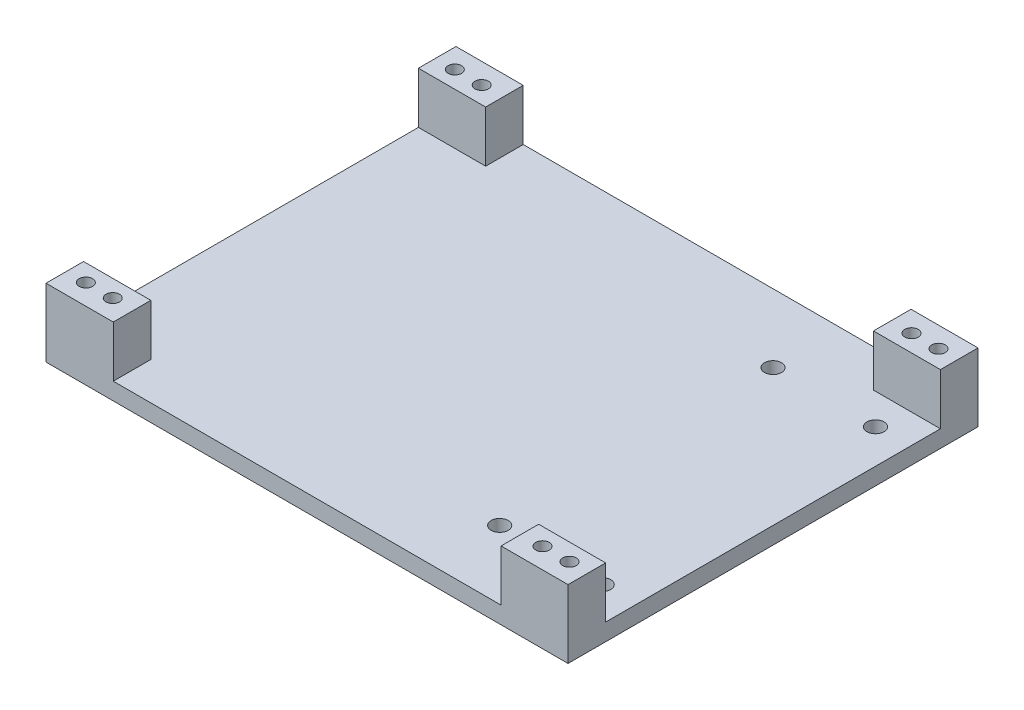
SolidWorks part; units mm, degrees
ref_plane "Front Plane" through (0, 0, 0) normal (0, 0, 1) x (1, 0, 0)
ref_plane "Top Plane" through (0, 0, 0) normal (0, 1, 0) x (1, 0, 0)
ref_plane "Right Plane" through (0, 0, 0) normal (1, 0, 0) x (0, 0, -1)
sketch "Sketch2" plane through (0, 0, 0) normal (0, 1, 0) x (1, 0, 0)
  line L1 (-140.716, 56.5856) -> (53.34, 56.5856)
  line L2 (-140.716, 56.5856) -> (-140.716, -95.8144)
  line L3 (-140.716, -95.8144) -> (53.34, -95.8144)
  line L4 (53.34, 56.5856) -> (53.34, -95.8144)
  dimension "D1" = 194.056
  dimension "D2" = 152.4
extrude "Boss-Extrude1" add sketch "Sketch2" along normal blind 6.35
sketch "Sketch3" plane through (0, 6.35, 0) normal (0, 1, 0) x (1, 0, 0)
  line L1 (53.34, -95.8144) -> (53.34, 56.5856) construction
  line L2 (-140.716, -95.8144) -> (53.34, -95.8144) construction
  line L3 (53.34, 56.5856) -> (-140.716, 56.5856) construction
  circle A0 centre (2.54, -70.4144) radius 3.175
  circle A1 centre (2.54, 31.1856) radius 3.175
  circle A2 centre (40.64, 31.1856) radius 3.175
  circle A3 centre (40.64, -70.4144) radius 3.175
  dimension "D1" = 6.35
  dimension "D2" = 38.1
  dimension "D3" = 12.7
  dimension "1" = 25.4
  dimension "D5" = 25.4
extrude "Cut-Extrude1" cut sketch "Sketch3" against normal blind 6.35
sketch "Sketch4" plane through (0, 6.35, 0) normal (0, 1, 0) x (1, 0, 0)
  line L1 (53.34, -95.8144) -> (28.448, -95.8144)
  line L2 (53.34, -95.8144) -> (53.34, -81.8444)
  line L3 (53.34, -81.8444) -> (28.448, -81.8444)
  line L4 (28.448, -95.8144) -> (28.448, -81.8444)
  line L5 (-140.716, -95.8144) -> (-115.716, -95.8144)
  line L6 (-140.716, -95.8144) -> (-140.716, -81.8444)
  line L7 (-140.716, -81.8444) -> (-115.716, -81.8444)
  line L8 (-115.716, -95.8144) -> (-115.716, -81.8444)
  line L9 (-140.716, 56.5856) -> (-115.716, 56.5856)
  line L10 (-140.716, 56.5856) -> (-140.716, 42.6156)
  line L11 (-140.716, 42.6156) -> (-115.716, 42.6156)
  line L12 (-115.716, 56.5856) -> (-115.716, 42.6156)
  line L13 (53.34, 56.5856) -> (28.448, 56.5856)
  line L14 (53.34, 56.5856) -> (53.34, 42.6156)
  line L15 (53.34, 42.6156) -> (28.448, 42.6156)
  line L16 (28.448, 56.5856) -> (28.448, 42.6156)
  dimension "D1" = 13.97
  dimension "1in" = 25
  dimension "D2" = 13.97
  dimension "D3" = 24.892
extrude "Boss-Extrude2" add sketch "Sketch4" along normal blind 19.05
sketch "Sketch5" plane through (0, 25.4, 0) normal (0, 1, 0) x (1, 0, 0)
  line L1 (-115.716, 56.5856) -> (-140.716, 56.5856) construction
  line L2 (-140.716, -95.8144) -> (-115.716, -95.8144) construction
  line L5 (53.34, 56.5856) -> (28.448, 56.5856) construction
  line L6 (28.448, -95.8144) -> (53.34, -95.8144) construction
  line L7 (-115.716, 42.6156) -> (-115.716, 56.5856) construction
  line L8 (28.448, 56.5856) -> (28.448, 42.6156) construction
  line L9 (28.448, -81.8444) -> (28.448, -95.8144) construction
  circle A0 centre (-133.526, -88.1944) radius 2.5
  circle A1 centre (-123.526, -88.1944) radius 2.5
  circle A2 centre (-133.526, 48.9656) radius 2.5
  circle A3 centre (-123.526, 48.9656) radius 2.5
  circle A4 centre (36.258, 48.9656) radius 2.5
  circle A5 centre (46.258, 48.9656) radius 2.5
  circle A6 centre (36.258, -88.1944) radius 2.5
  circle A7 centre (46.258, -88.1944) radius 2.5
  dimension "D1" = 5
  dimension "D8" = 10
  dimension "D12" = 7.81
  dimension "D2" = 7.81
  dimension "D3" = 10
  dimension "D4" = 10
  dimension "D5" = 7.62
  dimension "D6" = 7.62
  dimension "D7" = 10
  dimension "D9" = 7.81
  dimension "D10" = 7.62
  dimension "D11" = 7.62
extrude "Cut-Extrude2" cut sketch "Sketch5" against normal through all
